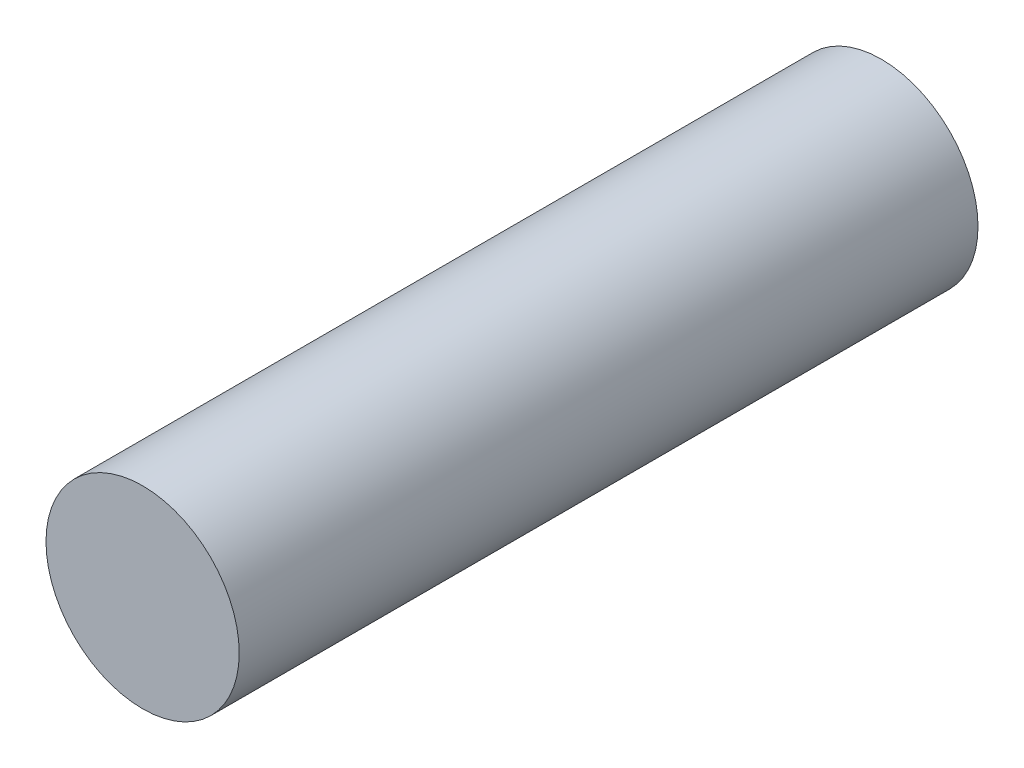
SolidWorks part; units mm, degrees
ref_plane "Front" through (0, 0, 0) normal (0, 0, 1) x (1, 0, 0)
ref_plane "Top" through (0, 0, 0) normal (0, 1, 0) x (1, 0, 0)
ref_plane "Right" through (0, 0, 0) normal (1, 0, 0) x (0, 0, -1)
sketch "Sketch1" plane through (0, 0, 0) normal (0, 0, 1) x (1, 0, 0)
  circle A0 centre (0, 0) radius 8.5
  dimension "D1" = 17
extrude "Boss-Extrude1" add sketch "Sketch1" along normal blind 65
